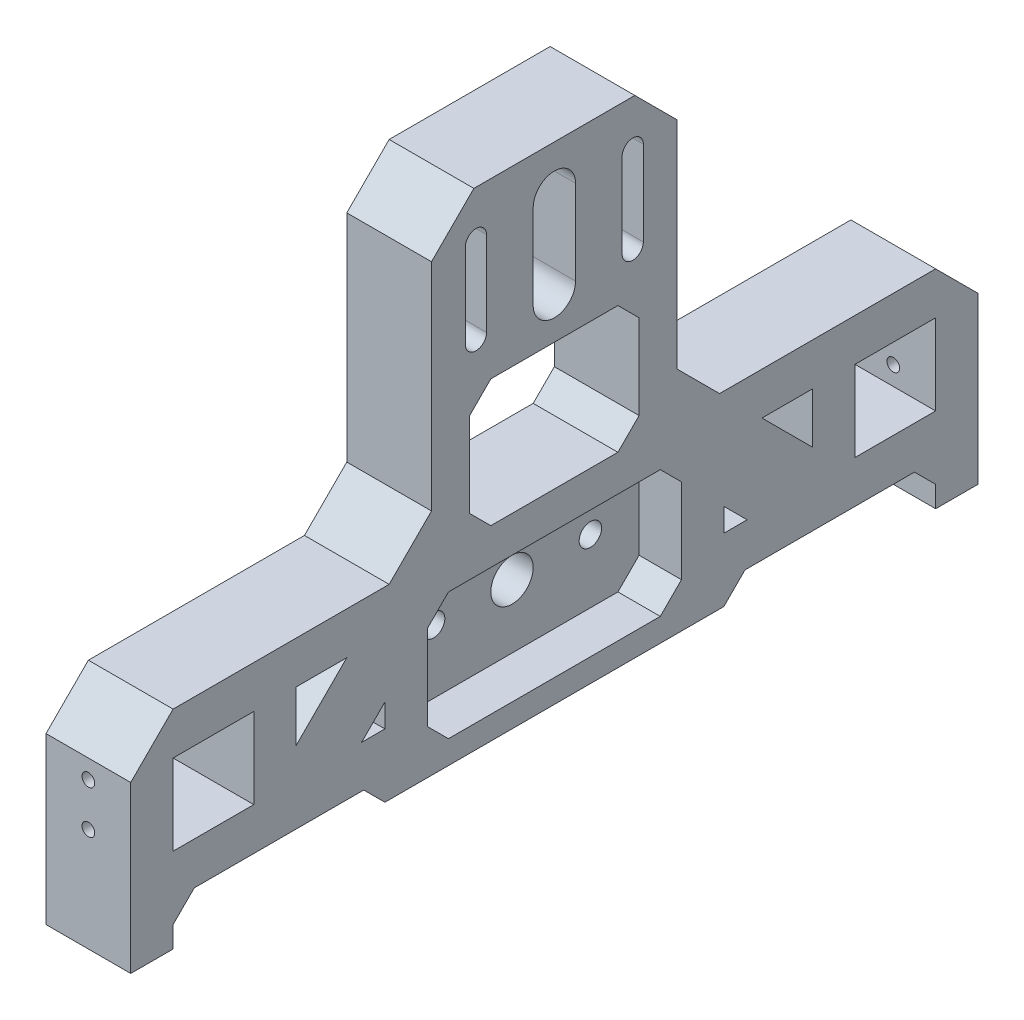
SolidWorks part; units mm, degrees
ref_plane "Front Plane" through (0, 0, 0) normal (0, 0, 1) x (1, 0, 0)
ref_plane "Top Plane" through (0, 0, 0) normal (0, 1, 0) x (1, 0, 0)
ref_plane "Right Plane" through (0, 0, 0) normal (1, 0, 0) x (0, 0, -1)
sketch "Sketch1" plane through (0, 0, 0) normal (1, 0, 0) x (0, 0, -1)
  line L1 (0, 0) -> (-100, 0)
  line L2 (0, 0) -> (0, 120)
  line L3 (0, 120) -> (-100, 120)
  line L4 (-100, 0) -> (-100, 120)
  dimension "D1" = 100
  dimension "D2" = 120
extrude "Boss-Extrude1" add sketch "Sketch1" along normal blind 20
sketch "Sketch2" plane through (20, 0, 0) normal (1, 0, 0) x (0, 0, -1)
  line L0 (-100, 0) -> (0, 0) construction
  line L1 (-90, 39.05) -> (-70.95, 39.05)
  line L2 (-90, 39.05) -> (-90, 20)
  line L3 (-90, 20) -> (-70.95, 20)
  line L4 (-70.95, 39.05) -> (-70.95, 20)
  line L5 (-100, 120) -> (-100, 0) construction
  dimension "D1" = 19.05
  dimension "D2" = 20
  dimension "D3" = 10
extrude "Cut-Extrude1" cut sketch "Sketch2" against normal blind 20
sketch "Sketch3" plane through (0, 0, 100) normal (0, 0, 1) x (1, 0, 0)
  line L0 (10, 34.605) -> (10, 24.445) construction
  line L1 (20, 39.05) -> (20, 20) construction
  line L2 (20, 0) -> (0, 0) construction
  circle A0 centre (10, 34.605) radius 1.5
  circle A1 centre (10, 24.445) radius 1.5
  point P6 (20, 29.525)
  point P7 (10, 29.525)
  point P10 (10, 0)
  dimension "D1" = 3
  dimension "D2" = 10.16
extrude "Cut-Extrude2" cut sketch "Sketch3" against normal blind 20
mirror "Mirror1" about plane through (20, 0, 0) normal (0, 0, 1) of "Cut-Extrude2", "Cut-Extrude1", "Boss-Extrude1"
sketch "Sketch5" plane through (20, 0, 0) normal (1, 0, 0) x (0, 0, -1)
  line L0 (0, 0) -> (0, 120) construction
  line L1 (-100, 0) -> (100, 0) construction
  line L2 (100, 120) -> (-100, 120) construction
  circle A0 centre (0, 25.5) radius 5
  circle A5 centre (-18.5, 25.5) radius 2.65
  circle A6 centre (18.5, 25.5) radius 2.65
  dimension "D1" = 10
  dimension "D2" = 5.3
  dimension "D3" = 18.5
  dimension "D4" = 25.5
extrude "Cut-Extrude3" cut sketch "Sketch5" against normal through all
sketch "Sketch6" plane through (20, 0, 0) normal (1, 0, 0) x (0, 0, -1)
  line L1 (30, 10.5) -> (-30, 10.5)
  line L2 (30, 10.5) -> (30, 40.5)
  line L3 (30, 40.5) -> (-30, 40.5)
  line L4 (-30, 10.5) -> (-30, 40.5)
  line L5 (30, 10.5) -> (-30, 40.5) construction
  line L6 (30, 40.5) -> (-30, 10.5) construction
  point P0 (0, 25.5)
  dimension "D1" = 30
  dimension "D2" = 60
extrude "Cut-Extrude4" cut sketch "Sketch6" against normal blind 10
sketch "Sketch7" plane through (20, 0, 0) normal (1, 0, 0) x (0, 0, -1)
  line L1 (0, 55) -> (0, -55) construction
  line L2 (-70.95, 39.05) -> (-90, 39.05) construction
  line B0 (5, 109.05) -> (5, 89.05)
  line B1 (0, 109.05) -> (0, 89.05) construction
  arc B2 (-5, 89.05) -> (5, 89.05) centre (0, 89.05) ccw
  line B3 (-5, 109.05) -> (-5, 89.05)
  arc B4 (5, 109.05) -> (-5, 109.05) centre (0, 109.05) ccw
  line B5 (-16, 109.05) -> (-16, 89.05)
  arc B6 (-21, 89.05) -> (-16, 89.05) centre (-18.5, 89.05) ccw
  line B7 (-21, 109.05) -> (-21, 89.05)
  arc B8 (-16, 109.05) -> (-21, 109.05) centre (-18.5, 109.05) ccw
  line B9 (16, 109.05) -> (16, 89.05)
  arc B10 (21, 89.05) -> (16, 89.05) centre (18.5, 89.05) cw
  line B11 (21, 109.05) -> (21, 89.05)
  arc B12 (16, 109.05) -> (21, 109.05) centre (18.5, 109.05) cw
  dimension "D1" = 60
sketch_block_instance "Block1-1"
sketch_block "Block1" parameters "D1"=10, "D2"=20, "D3"=5, "D4"=18.5
extrude "Cut-Extrude5" cut sketch "Sketch7" against normal through all
sketch "Sketch8" plane through (20, 0, 0) normal (1, 0, 0) x (0, 0, -1)
  line L0 (-21, 109.05) -> (-21, 89.05) construction
  line L1 (-100, 120) -> (-29, 120)
  line L2 (-100, 120) -> (-100, 49.05)
  line L3 (-100, 49.05) -> (-29, 49.05)
  line L4 (-29, 120) -> (-29, 49.05)
  line L5 (-70.95, 39.05) -> (-90, 39.05) construction
  line L6 (0, 55) -> (0, -55) construction
  line L7 (29, 120) -> (29, 49.05)
  line L8 (100, 49.05) -> (29, 49.05)
  line L9 (100, 120) -> (100, 49.05)
  line L10 (100, 120) -> (29, 120)
  dimension "D1" = 8
  dimension "D2" = 10
extrude "Cut-Extrude6" cut sketch "Sketch8" against normal through all
chamfer "Chamfer1" distance 10 angle 45 6 edges at (10, 49.05, 29) (10, 49.05, -29) (10, 49.05, 100) (10, 49.05, -100) (10, 120, -29) (10, 120, 29)
sketch "Sketch9" plane through (20, 0, 0) normal (1, 0, 0) x (0, 0, -1)
  line L0 (-100, 0) -> (100, 0) construction
  line L1 (-90, 0) -> (-40, 0)
  line L2 (-90, 0) -> (-90, 10)
  line L3 (-90, 10) -> (-40, 10)
  line L4 (-40, 0) -> (-40, 10)
  line L5 (-100, 39.05) -> (-100, 0) construction
  line L6 (-30, 40.5) -> (-30, 10.5) construction
  line L7 (-90, 20) -> (-70.95, 20) construction
  line L8 (0, 55) -> (0, -55) construction
  line L9 (40, 0) -> (40, 10)
  line L10 (90, 10) -> (40, 10)
  line L11 (90, 0) -> (90, 10)
  line L12 (90, 0) -> (40, 0)
  line L14 (-20, 79.05) -> (20, 79.05)
  line L15 (-20, 79.05) -> (-20, 49.05)
  line L16 (-20, 49.05) -> (20, 49.05)
  line L17 (20, 79.05) -> (20, 49.05)
  line L18 (-90, 49.05) -> (-39, 49.05) construction
  point P24 (0, 79.05)
  dimension "D1" = 10
  dimension "D2" = 10
  dimension "D3" = 10
  dimension "D4" = 40
  dimension "D5" = 30
extrude "Cut-Extrude7" cut sketch "Sketch9" against normal through all
chamfer "Chamfer2" distance 5 angle 45 12 edges at (10, 10, -90) (10, 10, -40) (10, 10, 40) (10, 10, 90) (10, 79.05, -20) (10, 49.05, -20) (10, 49.05, 20) (10, 79.05, 20) (15, 10.5, 30) (15, 10.5, -30) (15, 40.5, -30) (15, 40.5, 30)
sketch "Sketch11" plane through (20, 0, 0) normal (1, 0, 0) x (0, 0, -1)
  line L0 (-40, 25.5) -> (-45.5, 20)
  line L1 (-45.5, 20) -> (-40, 20)
  line L2 (-40, 20) -> (-40, 25.5)
  line L3 (-49, 39.05) -> (-60.95, 27.1)
  line L4 (-60.95, 27.1) -> (-60.95, 39.05)
  line L5 (-60.95, 39.05) -> (-49, 39.05)
  line L6 (-54.975, 39.05) -> (-54.975, 49.05) construction
  line L7 (-90, 49.05) -> (-39, 49.05) construction
  line L8 (-60.95, 33.075) -> (-70.95, 33.075) construction
  line L9 (-70.95, 20) -> (-70.95, 39.05) construction
  line L10 (-47.3495, 20) -> (-47.3495, 10) construction
  line L11 (-45, 10) -> (-85, 10) construction
  line L12 (-40, 22.75) -> (-30, 22.75) construction
  line L13 (-30, 35.5) -> (-30, 15.5) construction
  line L15 (-29, 59.05) -> (-39, 49.05) construction
  line L16 (-30, 35.5) -> (-25, 40.5) construction
  point P22 (-35, 22.75)
  dimension "D1" = 10
extrude "Cut-Extrude8" cut sketch "Sketch11" against normal through all
mirror "Mirror2" about plane through (0, 0, 0) normal (0, 0, 1) of "Cut-Extrude8"
sketch "Sketch12" plane through (0, 0, 0) normal (-1, 0, 0) x (0, 0, 1)
  line L0 (-40, 5) -> (-40, 0) construction
  line L1 (-40, 0) -> (40, 0)
  line L2 (-40, 0) -> (-40, 5)
  line L3 (-40, 5) -> (40, 5)
  line L4 (40, 0) -> (40, 5)
  line L5 (40, 0) -> (-40, 0) construction
extrude "Cut-Extrude9" cut sketch "Sketch12" against normal through all
